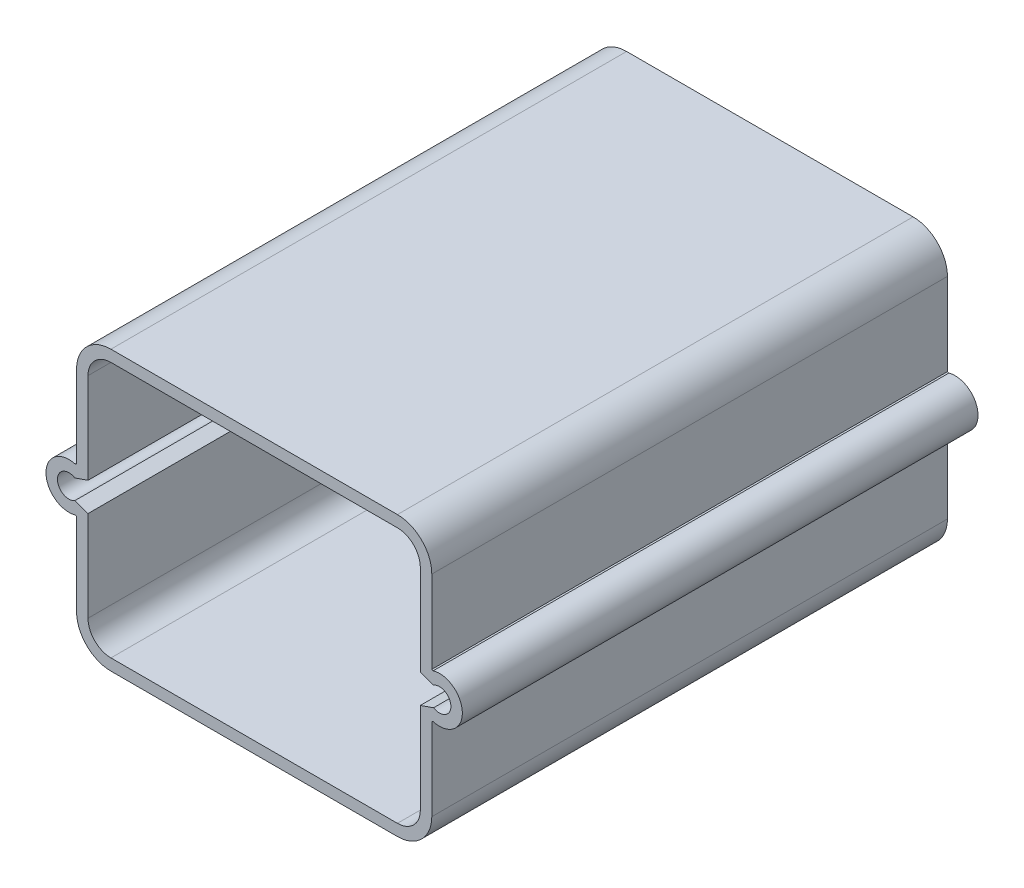
SolidWorks part; units mm, degrees
ref_plane "Front Plane" through (0, 0, 0) normal (0, 0, 1) x (1, 0, 0)
ref_plane "Top Plane" through (0, 0, 0) normal (0, 1, 0) x (1, 0, 0)
ref_plane "Right Plane" through (0, 0, 0) normal (1, 0, 0) x (0, 0, -1)
sketch "Sketch1-Slide_Rail_Reference" plane through (0, 0, 0) normal (0, 0, 1) x (1, 0, 0)
  line L0 (0, 30.2281) -> (0, -30.3143) construction
  line L1 (37.5, -32.5) -> (-37.5, -32.5)
  line L2 (42.5, -27.5) -> (42.5, -3.0589)
  line L3 (37.5, 32.5) -> (-37.5, 32.5)
  line L4 (-42.5, -27.5) -> (-42.5, -3.0589)
  line L5 (42.5, -32.5) -> (-42.5, 32.5) construction
  line L6 (42.5, 32.5) -> (-42.5, -32.5) construction
  line L7 (47.1293, 1.4564) -> (42.5, 3.0589)
  line L8 (-47.1293, -1.4564) -> (-42.5, -3.0589)
  line L9 (-38.2301, 0) -> (-48.5, 0) construction
  line L10 (-47.1293, 1.4564) -> (-42.5, 3.0589)
  line L11 (47.1293, -1.4564) -> (42.5, -3.0589)
  line L12 (-42.5, 3.0589) -> (-42.5, 27.5)
  line L13 (-25.1664, 0) -> (44.2513, 0) construction
  line L14 (42.5, 3.0589) -> (42.5, 27.5)
  line L16 (8.25, -2.625) -> (-8.25, -2.625)
  line L17 (8.25, -2.625) -> (8.25, 2.625)
  line L18 (8.25, 2.625) -> (-8.25, 2.625)
  line L19 (-8.25, -2.625) -> (-8.25, 2.625)
  line L20 (8.25, -2.625) -> (-8.25, 2.625) construction
  line L21 (8.25, 2.625) -> (-8.25, -2.625) construction
  arc A0 (-47.1293, 1.4564) -> (-47.1293, -1.4564) centre (-48.5, 0) ccw
  arc A1 (47.1293, 1.4564) -> (47.1293, -1.4564) centre (48.5, 0) cw
  arc A2 (-42.5, -27.5) -> (-37.5, -32.5) centre (-37.5, -27.5) ccw
  arc A3 (37.5, -32.5) -> (42.5, -27.5) centre (37.5, -27.5) ccw
  arc A4 (42.5, 27.5) -> (37.5, 32.5) centre (37.5, 27.5) ccw
  arc A5 (-37.5, 32.5) -> (-42.5, 27.5) centre (-37.5, 27.5) ccw
  point P0 (0, 0)
  point P33 (0, 0)
  dimension "D1" = 5
  dimension "D6" = 6
  dimension "2" = 2
  dimension "D2" = 16.5
  dimension "D3" = 5.25
  dimension "D4" = 85
  dimension "D5" = 65
sketch "Sketch2-Slide_Rail_Reference" plane through (0, 0, 0) normal (0, 0, 1) x (1, 0, 0)
  line L30 (37.5, 33.5) -> (-37.5, 33.5)
  line L31 (-43.5, 27.5) -> (-43.5, 3.771)
  line L32 (-43.5, 3.771) -> (-46.9586, 2.5737)
  line L33 (-46.9586, -2.5737) -> (-43.5, -3.771)
  line L34 (-43.5, -3.771) -> (-43.5, -27.5)
  line L35 (-37.5, -33.5) -> (37.5, -33.5)
  line L36 (43.5, -27.5) -> (43.5, -3.771)
  line L37 (43.5, -3.771) -> (46.9586, -2.5737)
  line L38 (46.9586, 2.5737) -> (43.5, 3.771)
  line L39 (43.5, 3.771) -> (43.5, 27.5)
  arc A6 (-46.9586, 2.5737) -> (-46.9586, -2.5737) centre (-48.5, 0) ccw
  arc A7 (46.9586, -2.5737) -> (46.9586, 2.5737) centre (48.5, 0) ccw
  arc A13 (-37.5, 33.5) -> (-43.5, 27.5) centre (-37.5, 27.5) ccw
  arc A15 (-43.5, -27.5) -> (-37.5, -33.5) centre (-37.5, -27.5) ccw
  arc A17 (37.5, -33.5) -> (43.5, -27.5) centre (37.5, -27.5) ccw
  arc A19 (43.5, 27.5) -> (37.5, 33.5) centre (37.5, 27.5) ccw
sketch "Sketch3-Slide_Rail_Reference" plane through (0, 0, 0) normal (0, 0, 1) x (1, 0, 0)
  line L31 (37.5, 33.5) -> (-37.5, 33.5)
  line L32 (-43.5, 27.5) -> (-43.5, 3.771)
  line L33 (-43.5, 3.771) -> (-46.9586, 2.5737)
  line L34 (-46.9586, -2.5737) -> (-43.5, -3.771)
  line L35 (-43.5, -3.771) -> (-43.5, -27.5)
  line L36 (-37.5, -33.5) -> (37.5, -33.5)
  line L37 (43.5, -27.5) -> (43.5, -3.771)
  line L38 (43.5, -3.771) -> (46.9586, -2.5737)
  line L39 (46.9586, 2.5737) -> (43.5, 3.771)
  line L40 (43.5, 3.771) -> (43.5, 27.5)
  line L61 (37.5, 32.5) -> (-37.5, 32.5)
  line L62 (42.5, 3.0589) -> (42.5, 27.5)
  line L63 (47.1293, 1.4564) -> (42.5, 3.0589)
  line L64 (42.5, -3.0589) -> (47.1293, -1.4564)
  line L65 (42.5, -27.5) -> (42.5, -3.0589)
  line L66 (-37.5, -32.5) -> (37.5, -32.5)
  line L67 (-42.5, -3.0589) -> (-42.5, -27.5)
  line L68 (-47.1293, -1.4564) -> (-42.5, -3.0589)
  line L69 (-42.5, 3.0589) -> (-47.1293, 1.4564)
  line L70 (-42.5, 27.5) -> (-42.5, 3.0589)
  arc A18 (-37.5, 33.5) -> (-43.5, 27.5) centre (-37.5, 27.5) ccw
  arc A19 (-46.9586, 2.5737) -> (-46.9586, -2.5737) centre (-48.5, 0) ccw
  arc A20 (-43.5, -27.5) -> (-37.5, -33.5) centre (-37.5, -27.5) ccw
  arc A21 (37.5, -33.5) -> (43.5, -27.5) centre (37.5, -27.5) ccw
  arc A22 (46.9586, -2.5737) -> (46.9586, 2.5737) centre (48.5, 0) ccw
  arc A23 (43.5, 27.5) -> (37.5, 33.5) centre (37.5, 27.5) ccw
  arc A36 (42.5, 27.5) -> (37.5, 32.5) centre (37.5, 27.5) ccw
  arc A37 (47.1293, -1.4564) -> (47.1293, 1.4564) centre (48.5, 0) ccw
  arc A38 (37.5, -32.5) -> (42.5, -27.5) centre (37.5, -27.5) ccw
  arc A39 (-42.5, -27.5) -> (-37.5, -32.5) centre (-37.5, -27.5) ccw
  arc A40 (-47.1293, 1.4564) -> (-47.1293, -1.4564) centre (-48.5, 0) ccw
  arc A41 (-37.5, 32.5) -> (-42.5, 27.5) centre (-37.5, 27.5) ccw
sketch "Sketch4-Slide_Rail_Reference" plane through (0, 0, 0) normal (0, 0, 1) x (1, 0, 0)
  line L0 (0, 39.7316) -> (0, -39.3225) construction
  line L2 (67.4976, 0) -> (-58.1911, 0) construction
  line L4 (-34.5741, 27.5) -> (-34.5741, 33.5)
  line L6 (-37.5, 24.5741) -> (-43.5, 24.5741)
  line L20 (43.5, 27.5) -> (43.5, 24.5741)
  line L21 (34.5741, 33.5) -> (37.5, 33.5)
  line L22 (-34.5741, 33.5) -> (-37.5, 33.5)
  line L24 (-43.5, 27.5) -> (-43.5, 24.5741)
  line L25 (37.5, 24.5741) -> (43.5, 24.5741)
  line L26 (34.5741, 27.5) -> (34.5741, 33.5)
  line L27 (34.5741, -27.5) -> (34.5741, -33.5)
  line L28 (37.5, -24.5741) -> (43.5, -24.5741)
  line L29 (-43.5, -27.5) -> (-43.5, -24.5741)
  line L30 (-34.5741, -33.5) -> (-37.5, -33.5)
  line L31 (34.5741, -33.5) -> (37.5, -33.5)
  line L32 (43.5, -27.5) -> (43.5, -24.5741)
  line L33 (-37.5, -24.5741) -> (-43.5, -24.5741)
  line L34 (-34.5741, -27.5) -> (-34.5741, -33.5)
  arc A0 (-37.5, 24.5741) -> (-34.5741, 27.5) centre (-37.5, 27.5) ccw
  circle A8 centre (-37.5, 27.5) radius 1.778
  arc A10 (-37.5, 33.5) -> (-43.5, 27.5) centre (-37.5, 27.5) ccw
  arc A11 (37.5, 33.5) -> (43.5, 27.5) centre (37.5, 27.5) cw
  circle A12 centre (37.5, 27.5) radius 1.778
  arc A13 (37.5, 24.5741) -> (34.5741, 27.5) centre (37.5, 27.5) cw
  arc A14 (37.5, -24.5741) -> (34.5741, -27.5) centre (37.5, -27.5) ccw
  circle A15 centre (37.5, -27.5) radius 1.778
  arc A16 (37.5, -33.5) -> (43.5, -27.5) centre (37.5, -27.5) ccw
  arc A17 (-37.5, -33.5) -> (-43.5, -27.5) centre (-37.5, -27.5) cw
  circle A18 centre (-37.5, -27.5) radius 1.778
  arc A19 (-37.5, -24.5741) -> (-34.5741, -27.5) centre (-37.5, -27.5) cw
  dimension "D2" = 3.556
inserted part "Slide_Rail_Reference"
sketch "Sketch4" plane through (0, 0, 0) normal (0, 0, 1) x (1, 0, 0)
  line L20 (37.5, 33.5) -> (-37.5, 33.5)
  line L21 (43.5, 3.771) -> (43.5, 27.5)
  line L22 (46.9586, 2.5737) -> (43.5, 3.771)
  line L23 (43.5, -3.771) -> (46.9586, -2.5737)
  line L24 (43.5, -27.5) -> (43.5, -3.771)
  line L25 (-37.5, -33.5) -> (37.5, -33.5)
  line L26 (-43.5, -3.771) -> (-43.5, -27.5)
  line L27 (-46.9586, -2.5737) -> (-43.5, -3.771)
  line L28 (-43.5, 3.771) -> (-46.9586, 2.5737)
  line L29 (-43.5, 27.5) -> (-43.5, 3.771)
  line L30 (37.5, 33.5) -> (-37.5, 33.5)
  line L31 (43.5, 3.771) -> (43.5, 27.5)
  line L32 (46.9586, 2.5737) -> (43.5, 3.771)
  line L33 (43.5, -3.771) -> (46.9586, -2.5737)
  line L34 (43.5, -27.5) -> (43.5, -3.771)
  line L35 (-37.5, -33.5) -> (37.5, -33.5)
  line L36 (-43.5, -3.771) -> (-43.5, -27.5)
  line L37 (-46.9586, -2.5737) -> (-43.5, -3.771)
  line L38 (-43.5, 3.771) -> (-46.9586, 2.5737)
  line L39 (-43.5, 27.5) -> (-43.5, 3.771)
  arc A12 (43.5, 27.5) -> (37.5, 33.5) centre (37.5, 27.5) ccw
  arc A13 (46.9586, -2.5737) -> (46.9586, 2.5737) centre (48.5, 0) ccw
  arc A14 (37.5, -33.5) -> (43.5, -27.5) centre (37.5, -27.5) ccw
  arc A15 (-43.5, -27.5) -> (-37.5, -33.5) centre (-37.5, -27.5) ccw
  arc A16 (-46.9586, 2.5737) -> (-46.9586, -2.5737) centre (-48.5, 0) ccw
  arc A17 (-37.5, 33.5) -> (-43.5, 27.5) centre (-37.5, 27.5) ccw
  arc A18 (43.5, 27.5) -> (37.5, 33.5) centre (37.5, 27.5) ccw
  arc A19 (46.9586, -2.5737) -> (46.9586, 2.5737) centre (48.5, 0) ccw
  arc A20 (37.5, -33.5) -> (43.5, -27.5) centre (37.5, -27.5) ccw
  arc A21 (-43.5, -27.5) -> (-37.5, -33.5) centre (-37.5, -27.5) ccw
  arc A22 (-46.9586, 2.5737) -> (-46.9586, -2.5737) centre (-48.5, 0) ccw
  arc A23 (-37.5, 33.5) -> (-43.5, 27.5) centre (-37.5, 27.5) ccw
  dimension "D1" = 0
extrude "Extrude-Thin1" add sketch "Sketch4" along normal blind 135 thin
sketch "Sketch5" plane through (0, 0, 0) normal (0, 0, -1) x (-1, 0, 0)
  line B0 (-31.5, 25.8301) -> (-31.5, 32.5)
  line B1 (-36.5, 20.8301) -> (-42.5, 20.8301)
  line B2 (67.4695, 0) -> (-65.0123, 0) construction
  line B3 (36.5, 20.8301) -> (42.5, 20.8301)
  line B4 (31.5, 25.8301) -> (31.5, 32.5)
  line B5 (31.5, -25.8301) -> (31.5, -32.5)
  line B6 (36.5, -20.8301) -> (42.5, -20.8301)
  line B7 (-36.5, -20.8301) -> (-42.5, -20.8301)
  line B8 (-31.5, -25.8301) -> (-31.5, -32.5)
  arc B9 (-36.5, 20.8301) -> (-31.5, 25.8301) centre (-36.5, 25.8301) ccw
  arc B10 (36.5, 20.8301) -> (31.5, 25.8301) centre (36.5, 25.8301) cw
  arc B11 (36.5, -20.8301) -> (31.5, -25.8301) centre (36.5, -25.8301) ccw
  arc B12 (-36.5, -20.8301) -> (-31.5, -25.8301) centre (-36.5, -25.8301) cw
  arc B13 (-37.5, 32.5) -> (-42.5, 27.5) centre (-37.5, 27.5) ccw
sketch_block_instance "Block-Slide_Magnet_Holder-1"
sketch_block "Block-Slide_Magnet_Holder"
sketch "Sketch6" plane through (0, 0, 0) normal (0, 0, -1) x (-1, 0, 0)
  line L677 (-31.5, 25.8301) -> (-31.5, 32.5)
  line L678 (-42.5, 20.8301) -> (-36.5, 20.8301)
  line L679 (-31.5, 25.8301) -> (-31.5, 33.5)
  line L680 (-43.5, 20.8301) -> (-36.5, 20.8301)
  line L682 (0, 56.6695) -> (0, -42.375) construction
  line L683 (83.7754, 0) -> (-77.6828, 0) construction
  line L684 (-43.5, 3.771) -> (-43.5, 27.5)
  line L685 (-37.5, 33.5) -> (37.5, 33.5)
  line L686 (-43.5, 20.8301) -> (-43.5, 27.5)
  line L687 (-37.5, 33.5) -> (-31.5, 33.5)
  line L688 (37.5, 33.5) -> (31.5, 33.5)
  line L689 (43.5, 20.8301) -> (43.5, 27.5)
  line L690 (43.5, 20.8301) -> (36.5, 20.8301)
  line L691 (31.5, 25.8301) -> (31.5, 33.5)
  line L692 (31.5, -25.8301) -> (31.5, -33.5)
  line L693 (43.5, -20.8301) -> (36.5, -20.8301)
  line L694 (43.5, -20.8301) -> (43.5, -27.5)
  line L695 (37.5, -33.5) -> (31.5, -33.5)
  line L696 (-37.5, -33.5) -> (-31.5, -33.5)
  line L697 (-43.5, -20.8301) -> (-43.5, -27.5)
  line L698 (-43.5, -20.8301) -> (-36.5, -20.8301)
  line L699 (-31.5, -25.8301) -> (-31.5, -33.5)
  arc A337 (-36.5, 20.8301) -> (-31.5, 25.8301) centre (-36.5, 25.8301) ccw
  arc A338 (-36.5, 20.8301) -> (-31.5, 25.8301) centre (-36.5, 25.8301) ccw
  circle A341 centre (-36.5, 25.8301) radius 3.429
  arc A342 (-37.5, 33.5) -> (-43.5, 27.5) centre (-37.5, 27.5) ccw
  arc A343 (-37.5, 33.5) -> (-43.5, 27.5) centre (-37.5, 27.5) ccw
  arc A344 (37.5, 33.5) -> (43.5, 27.5) centre (37.5, 27.5) cw
  circle A345 centre (36.5, 25.8301) radius 3.429
  arc A346 (36.5, 20.8301) -> (31.5, 25.8301) centre (36.5, 25.8301) cw
  arc A347 (36.5, -20.8301) -> (31.5, -25.8301) centre (36.5, -25.8301) ccw
  circle A348 centre (36.5, -25.8301) radius 3.429
  arc A349 (37.5, -33.5) -> (43.5, -27.5) centre (37.5, -27.5) ccw
  arc A350 (-37.5, -33.5) -> (-43.5, -27.5) centre (-37.5, -27.5) cw
  circle A351 centre (-36.5, -25.8301) radius 3.429
  arc A352 (-36.5, -20.8301) -> (-31.5, -25.8301) centre (-36.5, -25.8301) cw
  dimension "D3" = 6.858
  dimension "D1" = 0
  dimension "D2" = 0
extrude "Boss-Extrude1" add sketch "Sketch6" against normal blind 6
fillet "Fillet1" radius 1 12 edges at (31.5, -29.6651, 6) (32.9645, -22.2946, 6) (40, 20.8301, 6) (32.9645, 22.2946, 6) (-31.5, -29.6651, 6) (-40, -20.8301, 6) (-32.9645, -22.2946, 6) (-31.5, 29.6651, 6) (-32.9645, 22.2946, 6) (-40, 20.8301, 6) (40, -20.8301, 6) (31.5, 29.6651, 6)
